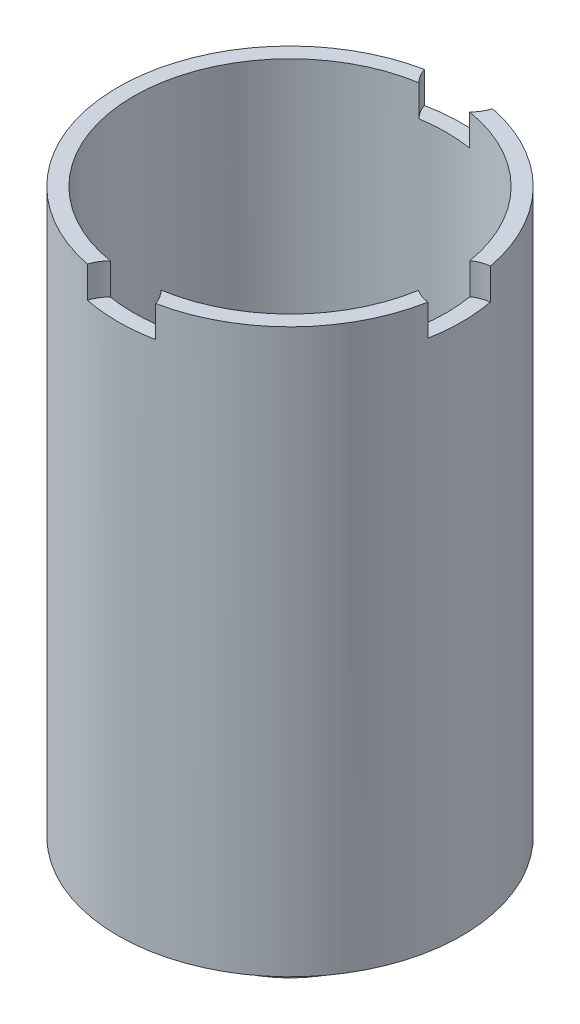
SolidWorks part; units mm, degrees
ref_plane "Face" through (0, 0, 0) normal (0, 0, 1) x (1, 0, 0)
ref_plane "Dessus" through (0, 0, 0) normal (0, 1, 0) x (1, 0, 0)
ref_plane "Droite" through (0, 0, 0) normal (1, 0, 0) x (0, 0, -1)
sketch "Esquisse1" plane through (0, 0, 0) normal (0, 1, 0) x (1, 0, 0)
  line L0 (0, 16) -> (0, -18) construction
  circle A2 centre (0, 0) radius 5.5
  dimension "D3" = 11
extrude "Base-Extrusion" add sketch "Esquisse1" against normal blind 18
sketch "Esquisse2" plane through (0, -18, 0) normal (0, -1, 0) x (1, 0, 0)
  circle A0 centre (0, 0) radius 3
  dimension "D1" = 6
extrude "Boss.-Extru.1" add sketch "Esquisse2" along normal blind 1.8
shell "Coque1" thickness 0.5
sketch "Esquisse3" plane through (0, -19.8, 0) normal (0, -1, 0) x (1, 0, 0)
  circle A0 centre (0, 0) radius 1.25
  dimension "D1" = 2.5
extrude "Enlèv. mat.-Extru.1" cut sketch "Esquisse3" against normal through all
sketch "Esquisse4" plane through (0, 0, 0) normal (0, -1, 0) x (1, 0, 0)
  line L0 (5.5, 0) -> (0, 0) construction
  circle A0 centre (5.5, 0) radius 1
  circle A1 centre (0, -5.75) radius 1.15
  circle A2 centre (0, 5.75) radius 1.15
  circle A3 centre (0, 0) radius 1.25 construction
  dimension "D1" = 11.5
  dimension "D2" = 2.3
  dimension "D3" = 2
  dimension "D4" = 5.5
extrude "Enlèv. mat.-Extru.2" cut sketch "Esquisse4" along normal blind 1
ref_plane "Plan2" through (0, -13.45, 0) normal (0, 1, 0) x (-1, 0, 0)
sketch "Esquisse5" plane through (0, -18, 0) normal (0, -1, 0) x (1, 0, 0)
  circle A0 centre (0, 4.1768) radius 0.5
  dimension "D1" = 1
extrude "Enlèv. mat.-Extru.3" cut sketch "Esquisse5" against normal up to next
pattern_circular "Répétition circulaire1" count 3 over 180 about axis through (0, 0, 0) along (0, 1, 0) of "Enlèv. mat.-Extru.3"
